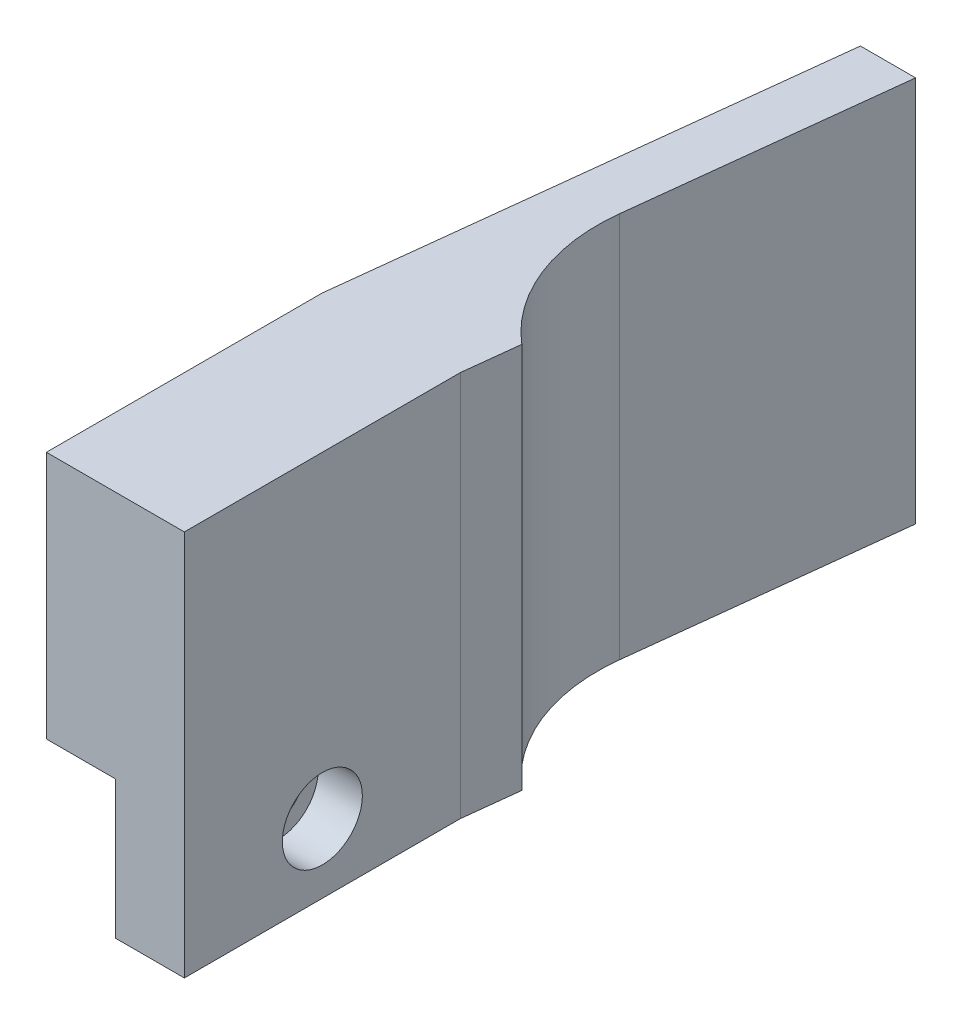
SolidWorks part; units mm, degrees
ref_plane "Front Plane" through (0, 0, 0) normal (0, 0, 1) x (1, 0, 0)
ref_plane "Top Plane" through (0, 0, 0) normal (0, 1, 0) x (1, 0, 0)
ref_plane "Right Plane" through (0, 0, 0) normal (1, 0, 0) x (0, 0, -1)
sketch "Profile" plane through (0, 0, 0) normal (0, 0, 1) x (1, 0, 0)
  line L1 (-6.35, 22.86) -> (6.35, 22.86)
  line L2 (-6.35, 22.86) -> (-6.35, 0)
  line L3 (-6.35, 0) -> (6.35, 0)
  line L4 (6.35, 22.86) -> (6.35, 0)
  line L5 (0, 0) -> (6.35, 0)
  line L6 (0, 0) -> (0, -12.7)
  line L7 (0, -12.7) -> (6.35, -12.7)
  line L8 (6.35, 0) -> (6.35, -12.7)
  dimension "D1" = 22.86
  dimension "D2" = 12.7
  dimension "D3" = 6.35
  dimension "D4" = 12.7
extrude "Boss-Extrude1" add sketch "Profile" along normal mid plane 25.4 contours L4 L1 L2 L3 | L8 L3 L6 L7
sketch "ScrewHole" plane through (0, 0, 0) normal (-1, 0, 0) x (0, 0, 1)
  line L0 (12.7, 0) -> (12.7, -12.7) construction
  line L1 (12.7, -12.7) -> (-12.7, -12.7) construction
  circle A0 centre (0, -6.35) radius 2.159
  point P5 (12.7, -6.35)
  point P10 (0, -12.7)
  dimension "D1" = 4.318
extrude "Cut-Extrude1" cut sketch "ScrewHole" against normal through all both
sketch "Sketch3" plane through (6.35, 0, 0) normal (1, 0, 0) x (0, 0, -1)
  circle A0 centre (0, -6.35) radius 2.159 construction
  circle A1 centre (0, -6.35) radius 2.159
  circle A2 centre (0, -6.35) radius 3.683
  dimension "D1" = 7.366
extrude "Cut-Extrude2" cut sketch "Sketch3" against normal blind 4.064
sketch "Sketch5" plane through (0, -12.7, 0) normal (0, -1, 0) x (1, 0, 0)
  line L0 (-6.35, 12.7) -> (-1.27, 57.15)
  line L1 (6.35, 12.7) -> (11.43, 57.15)
  line L2 (-6.35, 12.7) -> (0, 12.7) construction
  line L3 (-1.27, 57.15) -> (11.43, 57.15)
  line L4 (-6.35, 12.7) -> (6.35, 12.7)
  line L5 (3.81, 57.15) -> (1.0165, 32.7066)
  line L6 (-1000, 0) -> (49000, 0) construction
  line L7 (0, 12.7) -> (0, -12.7) construction
  line L8 (3.81, -57.15) -> (1.0165, -32.7066)
  line L9 (-6.35, -12.7) -> (6.35, -12.7)
  line L10 (-1.27, -57.15) -> (11.43, -57.15)
  line L11 (6.35, -12.7) -> (11.43, -57.15)
  line L12 (-6.35, -12.7) -> (-1.27, -57.15)
  arc A0 (1.0165, 32.7066) -> (6.9306, 17.78) centre (17.9313, 30.7735) ccw
  arc A1 (1.0165, -32.7066) -> (6.9306, -17.78) centre (17.9313, -30.7735) cw
  point P22 (0, 0)
  line M3 (0, -12.7) -> (6.35, -12.7)
  dimension "D5" = 17.0249
  dimension "D1" = 5.08
  dimension "D2" = 44.45
  dimension "D3" = 5.08
  dimension "D4" = 5.08
extrude "Boss-Extrude2" add sketch "Sketch5" against normal up to surface (35.56 mm away) contours L8 A1 L11 L9 L12 L10 M3 up to face at (0, 22.86, 0)
